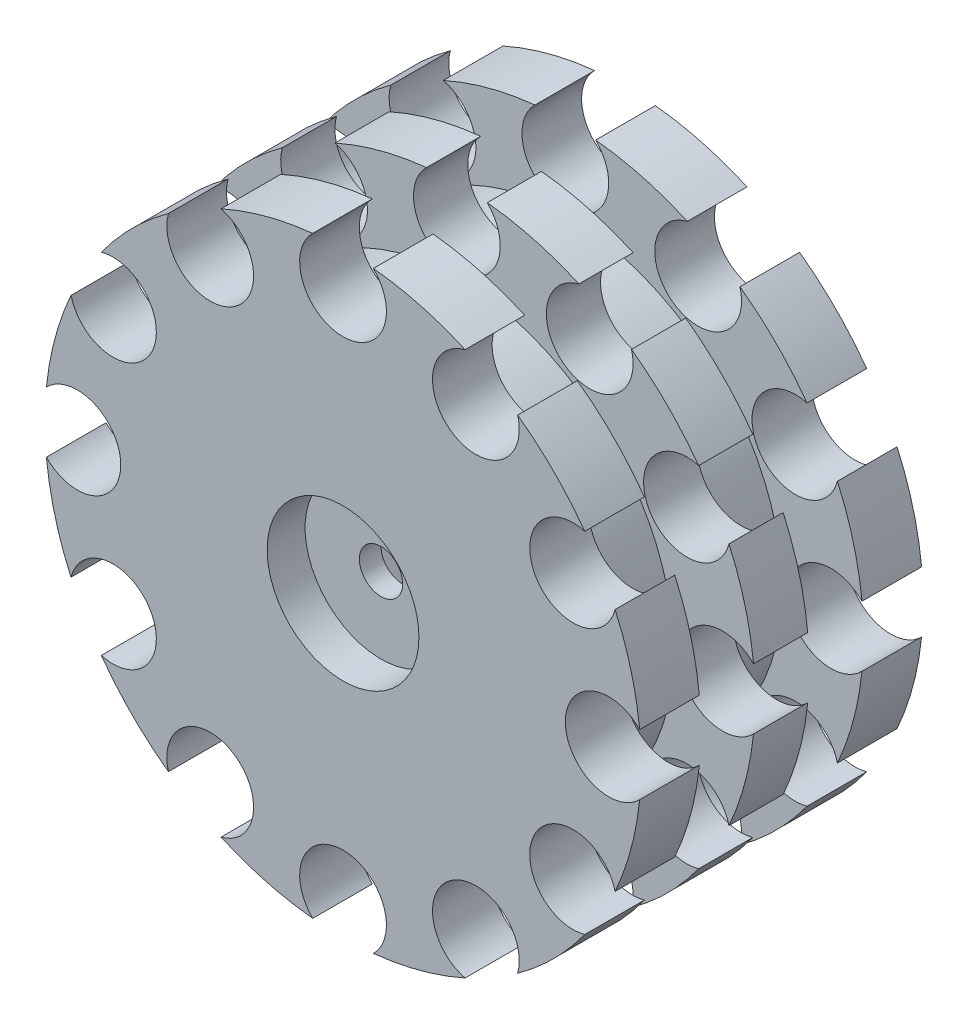
SolidWorks part; units mm, degrees
material "ABS"
ref_plane "Alzado" through (0, 0, 0) normal (0, 0, 1) x (1, 0, 0)
ref_plane "Planta" through (0, 0, 0) normal (0, 1, 0) x (1, 0, 0)
ref_plane "Vista lateral" through (0, 0, 0) normal (1, 0, 0) x (0, 0, -1)
sketch "Croquis1" plane through (0, 0, 0) normal (0, 1, 0) x (1, 0, 0)
  line L0 (0, 0) -> (0, 50000) construction
  line L1 (0, 1.5) -> (0, -9.5)
  line L3 (7, -9.5) -> (7, -13)
  line L4 (0, -9.5) -> (7, -9.5)
  line L5 (12.5, 13) -> (27.5, 13)
  line L6 (27.5, 13) -> (27.5, 7.5)
  line L7 (27.5, -2.5) -> (27.5, 2.5)
  line L8 (27.5, 2.5) -> (20, 2.5)
  line L9 (20, 2.5) -> (20, 7.5)
  line L10 (20, 7.5) -> (27.5, 7.5)
  line L12 (20, -7.5) -> (27.5, -7.5)
  line L13 (20, -2.5) -> (20, -7.5)
  line L14 (27.5, -2.5) -> (20, -2.5)
  line L15 (27.5, -13) -> (27.5, -7.5)
  line L16 (12.5, -13) -> (27.5, -13)
  line L27 (0, 1.5) -> (7.5, 1.5)
  line L28 (7.5, 1.5) -> (0, 1.5) construction
  line L29 (12.5, 6.5) -> (12.5, 13)
  line L32 (7, -13) -> (12.5, -13)
  line L37 (12.5, 6.5) -> (7.5, 1.5)
  line L38 (12.5, 6.5) -> (12.5, 13) construction
  point P22 (27.5, 0)
revolve "Revolución1" add sketch "Croquis1" angle 360 about L0
sketch "Croquis2" plane through (0, 0, -1.5) normal (0, 0, -1) x (-1, 0, 0)
  line L1 (7.5056, 0) -> (3.7528, 6.5)
  line L2 (3.7528, 6.5) -> (-3.7528, 6.5)
  line L3 (-3.7528, 6.5) -> (-7.5056, 0)
  line L4 (-7.5056, 0) -> (-3.7528, -6.5)
  line L5 (-3.7528, -6.5) -> (3.7528, -6.5)
  line L6 (3.7528, -6.5) -> (7.5056, 0)
  circle A0 centre (0, 0) radius 6.5 construction
extrude "Cortar-Extruir1" cut sketch "Croquis2" against normal blind 9
sketch "Croquis5" plane through (0, 0, 13) normal (0, 0, 1) x (1, 0, 0)
  line L0 (0, 0) -> (0, 27.5) construction
  line L1 (0, 27.5) -> (0, 24.5) construction
  circle A0 centre (0, 0) radius 27.5 construction
  circle A1 centre (0, 24.5) radius 4
  circle A2 centre (12.25, 21.2176) radius 4
  circle A3 centre (21.2176, 12.25) radius 4
  circle A4 centre (24.5, 0) radius 4
  circle A5 centre (21.2176, -12.25) radius 4
  circle A6 centre (12.25, -21.2176) radius 4
  circle A7 centre (0, -24.5) radius 4
  circle A8 centre (-12.25, -21.2176) radius 4
  circle A9 centre (-21.2176, -12.25) radius 4
  circle A10 centre (-24.5, 0) radius 4
  circle A11 centre (-21.2176, 12.25) radius 4
  circle A12 centre (-12.25, 21.2176) radius 4
  point P33 (0, 0)
  dimension "D1" = 12
extrude "Cortar-Extruir3" cut sketch "Croquis5" against normal through all
sketch "Croquis6" plane through (0, 0, 7.5) normal (0, 0, -1) x (-1, 0, 0)
  circle A0 centre (0, 0) radius 2
extrude "Cortar-Extruir4" cut sketch "Croquis6" against normal blind 10
